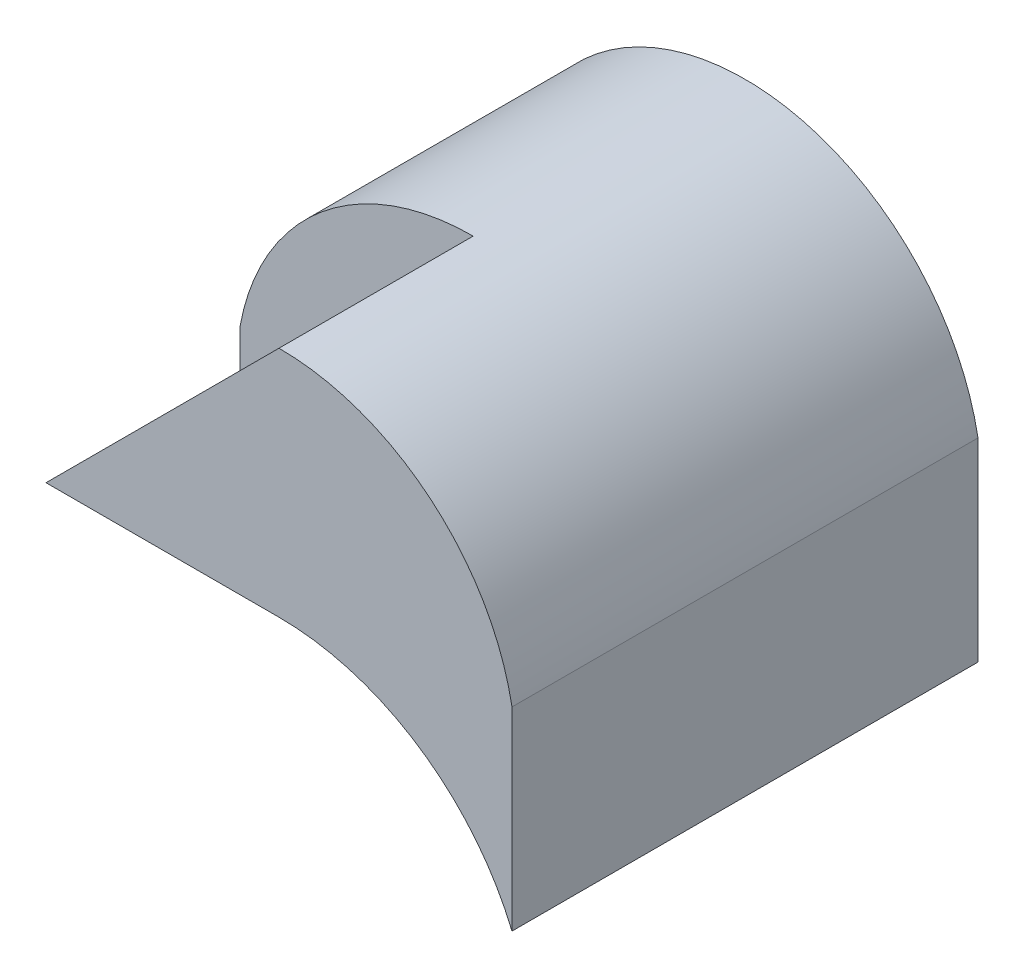
SolidWorks part; units mm, degrees
ref_plane "Front" through (0, 0, 0) normal (0, 0, 1) x (1, 0, 0)
ref_plane "Top" through (0, 0, 0) normal (0, 1, 0) x (1, 0, 0)
ref_plane "Right" through (0, 0, 0) normal (1, 0, 0) x (0, 0, -1)
sketch "Sketch1" plane through (0, 0, 0) normal (0, 1, 0) x (1, 0, 0)
  line L1 (-3, -3) -> (3, -3)
  line L2 (-3, -3) -> (-3, 3)
  line L3 (-3, 3) -> (3, 3)
  line L4 (3, -3) -> (3, 3)
  line L5 (-3, -3) -> (3, 3) construction
  line L6 (-3, 3) -> (3, -3) construction
  point P0 (0, 0)
  dimension "D1" = 6
  dimension "D2" = 6
extrude "Boss-Extrude1" add sketch "Sketch1" along normal blind 5
sketch "Sketch5" plane through (0, 0, 3) normal (0, 0, 1) x (1, 0, 0)
  line L0 (-3, 5) -> (-3, 0) construction
  line L1 (3, 5) -> (3, 0) construction
  line L6 (-3, 0) -> (3, 0)
  line L7 (3, 0) -> (3, 5)
  line L8 (3, 5) -> (-3, 5)
  line L9 (-3, 5) -> (-3, 0)
  line L10 (-3, 0) -> (3, 0)
  line L11 (3, 0) -> (3, 5)
  line L12 (3, 5) -> (-3, 5)
  line L13 (-3, 5) -> (-3, 0)
  arc A0 (-3, 0) -> (3, 0) centre (0, -1.25) cw
  arc A1 (-3, 2.5) -> (3, 2.5) centre (0, 1.95) cw
  point P8 (0, 2)
  point P14 (0, 5)
  line M5 (-3, 0) -> (3, 0)
  line M7 (3, 5) -> (-3, 5)
  line M8 (-3, 5) -> (-3, 0)
  dimension "D1" = 2
  dimension "D2" = 5
  dimension "D3" = 0
extrude "Cut-Extrude4" cut sketch "Sketch5" against normal blind 12.5 contours A1 L12 M8 | A1 L11 M7 | A0 M5
sketch "Sketch6" plane through (0, 0, 3) normal (0, 0, 1) x (1, 0, 0)
  line L0 (-3, 2.5) -> (-3, 0) construction
  line L1 (-3, 2) -> (0, 5)
  line L2 (-3, 2) -> (0, 2)
  line L3 (3, 0) -> (3, 2.5)
  line L4 (-3, 2.5) -> (-3, 0)
  line L5 (3, 0) -> (3, 2.5)
  line L6 (-3, 2.5) -> (-3, 0)
  arc A0 (-3, 2) -> (0, 5) centre (-3.55, 5.55) ccw
  arc A1 (3, 2.5) -> (-3, 2.5) centre (0, 1.95) ccw construction
  arc A4 (3, 2.5) -> (-3, 2.5) centre (0, 1.95) ccw
  arc A5 (3, 0) -> (-3, 0) centre (0, -1.25) ccw
  arc A6 (3, 2.5) -> (-3, 2.5) centre (0, 1.95) ccw
  arc A7 (3, 0) -> (-3, 0) centre (0, -1.25) ccw
  arc M6 (3, 2.5) -> (-3, 2.5) centre (0, 1.95) ccw
  line M7 (-3, 2.5) -> (-3, 0)
  arc M8 (-3, 0) -> (3, 0) centre (0, -1.25) cw
  dimension "D1" = 2
  dimension "D2" = 0
extrude "Cut-Extrude5" cut sketch "Sketch6" against normal blind 2.5 contours L1 M7 M6 | L2 M7 M8 | L5 A6 L6 A7
